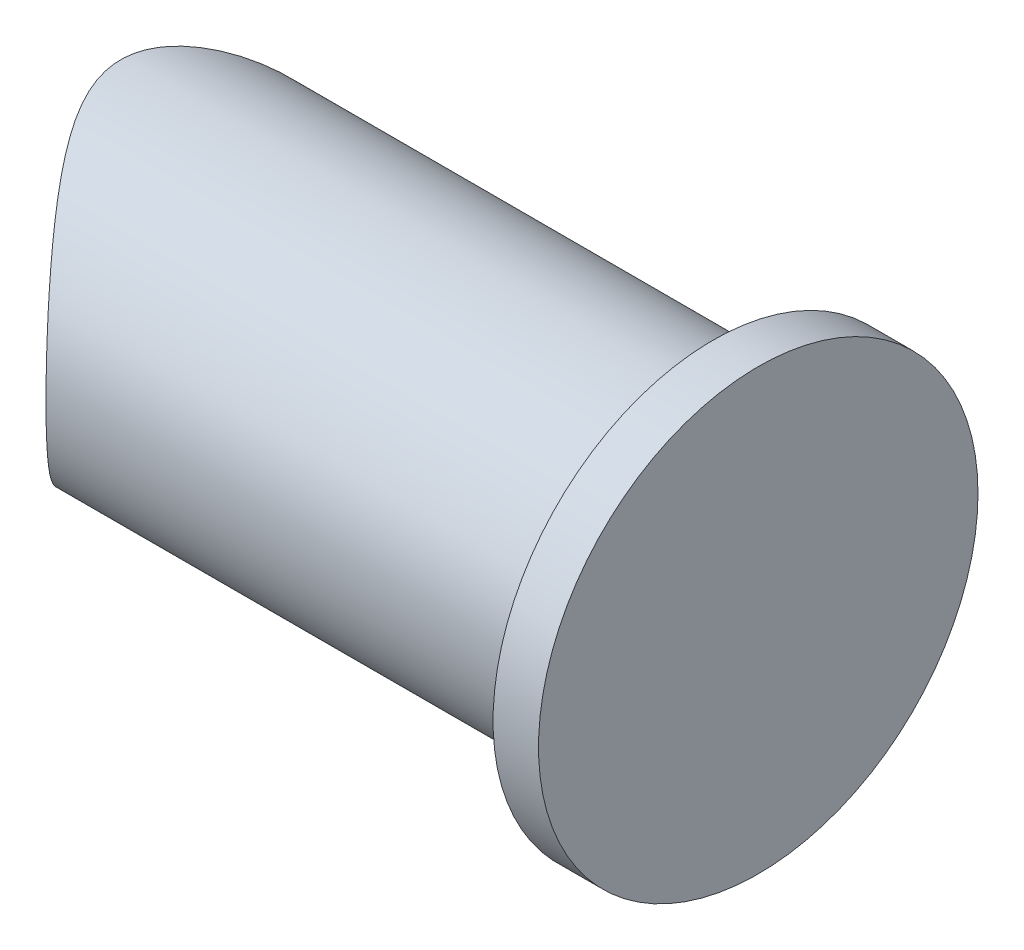
SolidWorks part; units mm, degrees
ref_plane "Plano frontal" through (0, 0, 0) normal (0, 0, 1) x (1, 0, 0)
ref_plane "Plano superior" through (0, 0, 0) normal (0, 1, 0) x (1, 0, 0)
ref_plane "Plano direito" through (0, 0, 0) normal (1, 0, 0) x (0, 0, -1)
sketch "Esboço1" plane through (0, 0, 0) normal (1, 0, 0) x (0, 0, -1)
  circle A0 centre (0, 0) radius 11
  dimension "D1" = 22
extrude "Extrusão1" add sketch "Esboço1" against normal blind 50
sketch "Esboço2" plane through (0, 0, 0) normal (0, 0, 1) x (1, 0, 0)
  circle A0 centre (-46, 0) radius 13
  dimension "D1" = 26
  dimension "D2" = 46
extrude "Corte-extrusão1" cut sketch "Esboço2" against normal mid plane 80
sketch "Esboço3" plane through (0, 0, 0) normal (1, 0, 0) x (0, 0, -1)
  circle A0 centre (0, 0) radius 14.5
  dimension "D1" = 29
extrude "Extrusão2" add sketch "Esboço3" along normal blind 3
